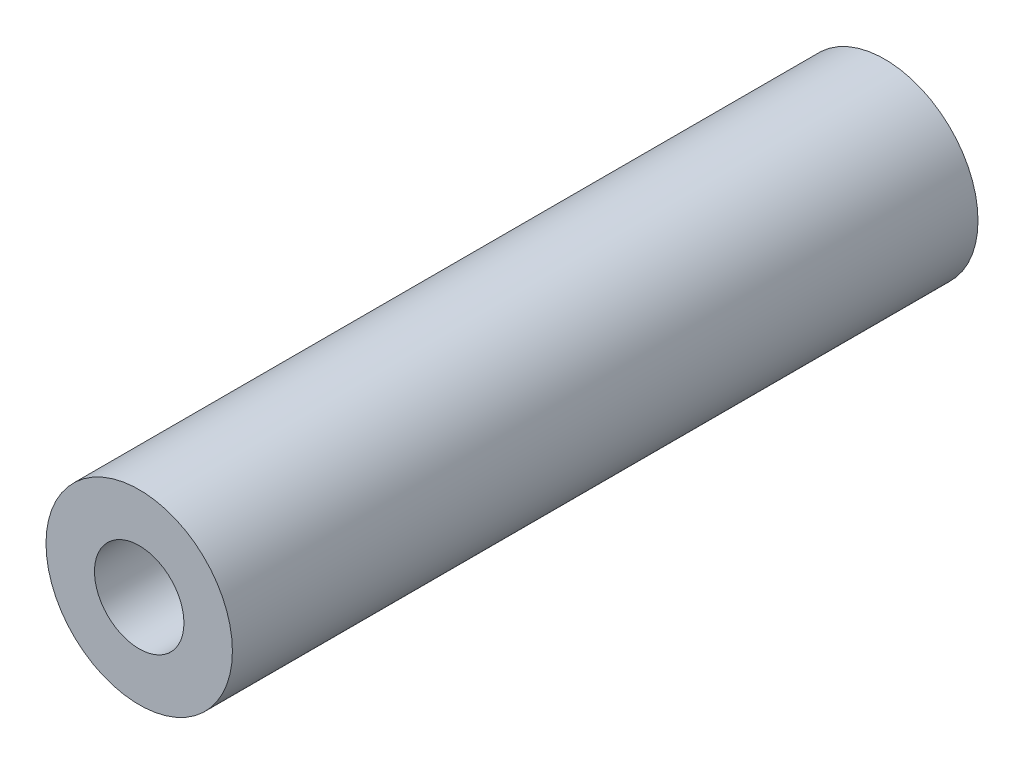
SolidWorks part; units mm, degrees
ref_plane "Front Plane" through (0, 0, 0) normal (0, 0, 1) x (1, 0, 0)
ref_plane "Top Plane" through (0, 0, 0) normal (0, 1, 0) x (1, 0, 0)
ref_plane "Right Plane" through (0, 0, 0) normal (1, 0, 0) x (0, 0, -1)
sketch "Sketch1" plane through (0, 0, 0) normal (0, 0, 1) x (1, 0, 0)
  circle A0 centre (0, 0) radius 3.175
  circle A1 centre (0, 0) radius 1.524
  dimension "D1" = 6.35
  dimension "D2" = 3.048
extrude "Extrude1" add sketch "Sketch1" along normal blind 25.4
